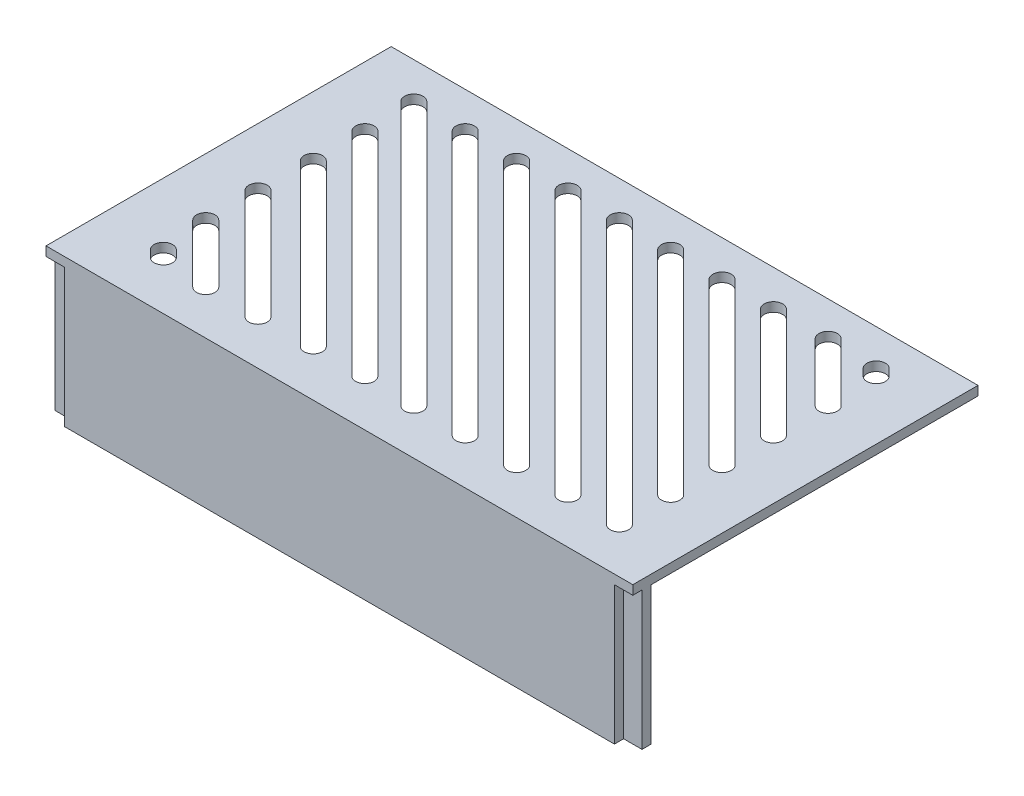
SolidWorks part; units mm, degrees
ref_plane "Front Plane" through (0, 0, 0) normal (0, 0, 1) x (1, 0, 0)
ref_plane "Top Plane" through (0, 0, 0) normal (0, 1, 0) x (1, 0, 0)
ref_plane "Right Plane" through (0, 0, 0) normal (1, 0, 0) x (0, 0, -1)
sketch "Sketch1" plane through (0, 0, 0) normal (0, 1, 0) x (1, 0, 0)
  line L1 (-31.875, -18.25) -> (31.875, -18.25)
  line L2 (-31.875, -18.25) -> (-31.875, 18.25)
  line L3 (-31.875, 18.25) -> (31.875, 18.25)
  line L4 (31.875, -18.25) -> (31.875, 18.25)
  line L5 (0, 18.25) -> (0, -18.25) construction
  line L6 (-31.875, 0) -> (31.875, 0) construction
  point P0 (0, 0)
  dimension "D1" = 63.75
  dimension "D2" = 36.5
extrude "Boss-Extrude1" add sketch "Sketch1" against normal blind 1
sketch "Sketch2" plane through (0, -1, 0) normal (0, -1, 0) x (-1, 0, 0)
  line L0 (-31.875, -18.25) -> (-31.875, 18.25) construction
  line L1 (31.875, -18.25) -> (-31.875, -18.25)
  line L2 (31.875, -18.25) -> (31.875, -17.25)
  line L3 (31.875, -17.25) -> (-31.875, -17.25)
  line L4 (-31.875, -18.25) -> (-31.875, -17.25)
  dimension "D1" = 1
extrude "Boss-Extrude2" add sketch "Sketch2" along normal up to vertex (15 mm away)
sketch "Sketch3" plane through (0, 0, 18.25) normal (0, 0, 1) x (1, 0, 0)
  line L0 (-31.875, 0) -> (31.875, 0)
  line L1 (31.875, 0) -> (31.875, -1)
  line L2 (31.875, -16) -> (31.875, 0) construction
  line L3 (29.875, -1) -> (31.875, -1) construction
  line L4 (31.875, -1) -> (29.875, -1)
  line L5 (29.875, -1) -> (29.875, -16)
  line L6 (29.875, -16) -> (-29.875, -16)
  line L7 (-29.875, -16) -> (-29.875, -1)
  line L8 (-29.875, -1) -> (-31.875, -1)
  line L9 (-31.875, -16) -> (-31.875, 0) construction
  line L10 (-29.875, -1) -> (-31.875, -1) construction
  line L11 (-31.875, -1) -> (-31.875, 0)
extrude "Boss-Extrude3" add sketch "Sketch3" along normal blind 1
sketch "Sketch4" plane through (0, 0, 0) normal (0, 1, 0) x (1, 0, 0)
  line L0 (0, 0) -> (-14.3093, 14.3093) construction
  line L7 (-25.4771, -14.3093) -> (25.4771, -14.3093) construction
  line L9 (0, -14.3093) -> (0, 14.3093) construction
  line L10 (-25.4771, 0) -> (25.4771, 0) construction
  line L11 (0, 0) -> (14.3093, -14.3093) construction
  line L12 (-25.4771, 14.3093) -> (3.1415, -14.3093)
  line L13 (-25.4771, -14.3093) -> (-25.4771, 14.3093) construction
  line L14 (-19.8932, 14.3093) -> (8.7254, -14.3093)
  line L15 (25.4771, 14.3093) -> (-25.4771, 14.3093) construction
  line L16 (25.4771, -14.3093) -> (25.4771, 14.3093) construction
  line L17 (5.58, 0) -> (-8.7293, 14.3093) construction
  line L18 (5.58, 0) -> (19.8893, -14.3093) construction
  line L19 (11.16, 0) -> (-3.1493, 14.3093) construction
  line L20 (11.16, 0) -> (25.4693, -14.3093) construction
  line L21 (16.74, 0) -> (2.4307, 14.3093) construction
  line L22 (22.32, 0) -> (8.0107, 14.3093) construction
  line L23 (16.74, 0) -> (25.4771, -8.7371) construction
  line L24 (22.32, 0) -> (25.4771, -3.1571) construction
  line L25 (-25.1327, -13.2463) -> (-24.4141, -13.9649) construction
  line L26 (-24.4256, -12.5391) -> (-23.707, -13.2577)
  line L27 (-25.8398, -13.9534) -> (-25.1212, -14.672)
  line L28 (13.5907, 14.3093) -> (25.4771, 2.4229)
  line L29 (19.3563, 14.4949) -> (25.6628, 8.1885)
  line L30 (24.7507, 14.3093) -> (25.4771, 13.5829)
  line L31 (-14.3093, 14.3093) -> (14.3093, -14.3093)
  line L32 (-8.7293, 14.3093) -> (19.8893, -14.3093)
  line L33 (-3.1493, 14.3093) -> (25.4771, -14.3093)
  line L34 (2.4307, 14.3093) -> (25.4771, -8.7371)
  line L35 (8.0107, 14.3093) -> (25.4771, -3.1571)
  line L36 (-25.618, -8.1516) -> (-19.3194, -14.4502) construction
  line L37 (-24.9109, -7.4445) -> (-18.6123, -13.7431)
  line L38 (-26.3251, -8.8587) -> (-20.0265, -15.1573)
  line L39 (-25.5696, -2.5232) -> (-13.691, -14.4018) construction
  line L40 (-24.8625, -1.8161) -> (-12.9839, -13.6947)
  line L41 (-26.2767, -3.2303) -> (-14.3981, -15.1089)
  line L42 (-2.3058, -14.1765) -> (-25.3444, 8.8621)
  line L43 (-7.899, -14.1898) -> (-25.3576, 3.2688)
  line L44 (-13.691, -14.4018) -> (-25.5696, -2.5232)
  line L45 (-19.3194, -14.4502) -> (-25.618, -8.1516)
  line L46 (-24.4141, -13.9649) -> (-25.1327, -13.2463)
  line L47 (-25.3576, 3.2688) -> (-7.899, -14.1898) construction
  line L48 (-24.6505, 3.9759) -> (-7.1919, -13.4827)
  line L49 (-26.0647, 2.5617) -> (-8.6061, -14.8969)
  line L50 (-25.3444, 8.8621) -> (-2.3058, -14.1765) construction
  line L51 (-24.6373, 9.5692) -> (-1.5986, -13.4694)
  line L52 (-26.0515, 8.1549) -> (-3.0129, -14.8837)
  line L53 (-25.4771, 14.3093) -> (3.1415, -14.3093) construction
  line L54 (-24.77, 15.0164) -> (3.8486, -13.6022)
  line L55 (-26.1842, 13.6022) -> (2.4344, -15.0164)
  line L56 (-19.8932, 14.3093) -> (8.7254, -14.3093) construction
  line L57 (-19.1861, 15.0164) -> (9.4325, -13.6022)
  line L58 (-20.6003, 13.6022) -> (8.0183, -15.0164)
  line L59 (-14.3093, 14.3093) -> (14.3093, -14.3093) construction
  line L60 (-13.6022, 15.0164) -> (15.0164, -13.6022)
  line L61 (-15.0164, 13.6022) -> (13.6022, -15.0164)
  line L62 (-8.7293, 14.3093) -> (19.8893, -14.3093) construction
  line L63 (-8.0222, 15.0164) -> (20.5964, -13.6022)
  line L64 (-9.4364, 13.6022) -> (19.1822, -15.0164)
  line L65 (-3.1493, 14.3093) -> (25.4771, -14.3093) construction
  line L66 (-2.4423, 15.0165) -> (26.1841, -13.6021)
  line L67 (-3.8563, 13.6021) -> (24.7701, -15.0165)
  line L68 (2.4307, 14.3093) -> (25.4771, -8.7371) construction
  line L69 (3.1378, 15.0164) -> (26.1842, -8.03)
  line L70 (1.7236, 13.6022) -> (24.77, -9.4442)
  line L71 (8.0107, 14.3093) -> (25.4771, -3.1571) construction
  line L72 (8.7178, 15.0164) -> (26.1842, -2.45)
  line L73 (7.3036, 13.6022) -> (24.77, -3.8642)
  line L74 (13.5907, 14.3093) -> (25.4771, 2.4229) construction
  line L75 (14.2978, 15.0164) -> (26.1842, 3.13)
  line L76 (12.8836, 13.6022) -> (24.77, 1.7158)
  line L77 (19.3563, 14.4949) -> (25.6628, 8.1885) construction
  line L78 (20.0634, 15.2021) -> (26.3699, 8.8956)
  line L79 (18.6492, 13.7878) -> (24.9557, 7.4814)
  line L80 (24.7507, 14.3093) -> (25.4771, 13.5829) construction
  line L81 (25.4578, 15.0164) -> (26.1842, 14.29)
  line L82 (24.0436, 13.6022) -> (24.77, 12.8758)
  arc A0 (-24.4256, -12.5391) -> (-25.8398, -13.9534) centre (-25.1327, -13.2463) ccw
  arc A1 (-25.1212, -14.672) -> (-23.707, -13.2577) centre (-24.4141, -13.9649) ccw
  arc A2 (-24.9109, -7.4445) -> (-26.3251, -8.8587) centre (-25.618, -8.1516) ccw
  arc A3 (-20.0265, -15.1573) -> (-18.6123, -13.7431) centre (-19.3194, -14.4502) ccw
  arc A4 (-24.8625, -1.8161) -> (-26.2767, -3.2303) centre (-25.5696, -2.5232) ccw
  arc A5 (-14.3981, -15.1089) -> (-12.9839, -13.6947) centre (-13.691, -14.4018) ccw
  arc A6 (-24.6505, 3.9759) -> (-26.0647, 2.5617) centre (-25.3576, 3.2688) ccw
  arc A7 (-8.6061, -14.8969) -> (-7.1919, -13.4827) centre (-7.899, -14.1898) ccw
  arc A8 (-24.6373, 9.5692) -> (-26.0515, 8.1549) centre (-25.3444, 8.8621) ccw
  arc A9 (-3.0129, -14.8837) -> (-1.5986, -13.4694) centre (-2.3058, -14.1765) ccw
  arc A10 (-24.77, 15.0164) -> (-26.1842, 13.6022) centre (-25.4771, 14.3093) ccw
  arc A11 (2.4344, -15.0164) -> (3.8486, -13.6022) centre (3.1415, -14.3093) ccw
  arc A12 (-19.1861, 15.0164) -> (-20.6003, 13.6022) centre (-19.8932, 14.3093) ccw
  arc A13 (8.0183, -15.0164) -> (9.4325, -13.6022) centre (8.7254, -14.3093) ccw
  arc A14 (-13.6022, 15.0164) -> (-15.0164, 13.6022) centre (-14.3093, 14.3093) ccw
  arc A15 (13.6022, -15.0164) -> (15.0164, -13.6022) centre (14.3093, -14.3093) ccw
  arc A16 (-8.0222, 15.0164) -> (-9.4364, 13.6022) centre (-8.7293, 14.3093) ccw
  arc A17 (19.1822, -15.0164) -> (20.5964, -13.6022) centre (19.8893, -14.3093) ccw
  arc A18 (-2.4423, 15.0165) -> (-3.8563, 13.6021) centre (-3.1493, 14.3093) ccw
  arc A19 (24.7701, -15.0165) -> (26.1841, -13.6021) centre (25.4771, -14.3093) ccw
  arc A20 (3.1378, 15.0164) -> (1.7236, 13.6022) centre (2.4307, 14.3093) ccw
  arc A21 (24.77, -9.4442) -> (26.1842, -8.03) centre (25.4771, -8.7371) ccw
  arc A22 (8.7178, 15.0164) -> (7.3036, 13.6022) centre (8.0107, 14.3093) ccw
  arc A23 (24.77, -3.8642) -> (26.1842, -2.45) centre (25.4771, -3.1571) ccw
  arc A24 (14.2978, 15.0164) -> (12.8836, 13.6022) centre (13.5907, 14.3093) ccw
  arc A25 (24.77, 1.7158) -> (26.1842, 3.13) centre (25.4771, 2.4229) ccw
  arc A26 (20.0634, 15.2021) -> (18.6492, 13.7878) centre (19.3563, 14.4949) ccw
  arc A27 (24.9557, 7.4814) -> (26.3699, 8.8956) centre (25.6628, 8.1885) ccw
  arc A28 (25.4578, 15.0164) -> (24.0436, 13.6022) centre (24.7507, 14.3093) ccw
  arc A29 (24.77, 12.8758) -> (26.1842, 14.29) centre (25.4771, 13.5829) ccw
  point P0 (0, 0)
  point P1 (0, 0)
  point P11 (-24.7734, -13.6056)
  point P36 (-22.4687, -11.3009)
  point P45 (-19.6303, -8.4625)
  point P55 (-16.6283, -5.4605)
  point P60 (-13.8251, -2.6572)
  point P65 (-11.1678, 0)
  point P70 (-5.5839, 0)
  point P75 (0, 0)
  point P80 (5.58, 0)
  point P85 (11.1639, 0)
  point P90 (13.9539, 2.7861)
  point P95 (16.7439, 5.5761)
  point P100 (19.5339, 8.3661)
  point P105 (22.5095, 11.3417)
  point P110 (25.1139, 13.9461)
  point P115 (-23.707, -14.672)
  dimension "D1" = 3
  dimension "D2" = 3
  dimension "D3" = 2
extrude "Cut-Extrude1" cut sketch "Sketch4" against normal up to next
